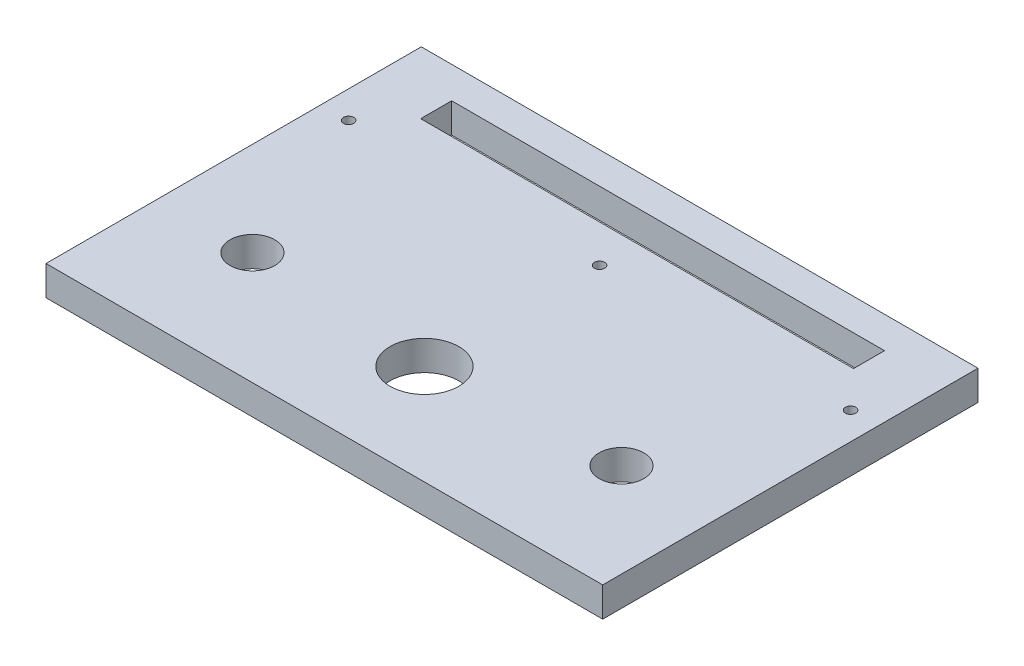
SolidWorks part; units mm, degrees
ref_plane "Front Plane" through (0, 0, 0) normal (0, 0, 1) x (1, 0, 0)
ref_plane "Top Plane" through (0, 0, 0) normal (0, 1, 0) x (1, 0, 0)
ref_plane "Right Plane" through (0, 0, 0) normal (1, 0, 0) x (0, 0, -1)
sketch "Sketch1" plane through (0, 0, 0) normal (0, 1, 0) x (1, 0, 0)
  line L2 (-89, 60) -> (-89, -60)
  line L3 (-89, -60) -> (89, -60)
  line L4 (89, 60) -> (89, -60)
  line L5 (-89, 60) -> (89, -60) construction
  line L6 (-89, -60) -> (89, 60) construction
  line L10 (0, 60) -> (0, -60) construction
  line L11 (-89, 60) -> (89, 60)
  line L12 (-69.2, 49.9) -> (-69.2, 40)
  line L13 (-69.2, 40) -> (69.2, 40)
  line L14 (69.2, 40) -> (69.2, 49.9)
  line L15 (69.2, 49.9) -> (-69.2, 49.9)
  circle A0 centre (0, -28) radius 11
  circle A1 centre (-59, -24) radius 7.15
  circle A2 centre (59, -24) radius 7.15
  point P0 (0, 0)
  point P19 (0, 49.9)
  dimension "D5" = 22
  dimension "D7" = 14.3
  dimension "D8" = 59
  dimension "D9" = 4
  dimension "D1" = 178
  dimension "D2" = 120
  dimension "D3" = 20
  dimension "D4" = 9.9
  dimension "D6" = 36
  dimension "D10" = 138.4
extrude "Boss-Extrude1" add sketch "Sketch1" along normal blind 9.5
hole_wizard "M4 Tapped Hole1" positions "Sketch2" profile "Sketch3" tap size "M4" standard "ISO" end condition through all
sketch "Sketch2" plane through (0, 9.5, 0) normal (0, 1, 0) x (1, 0, 0)
  line L0 (0, 60) -> (0, -60) construction
  line L3 (-89, 60) -> (-89, -60) construction
  line L5 (89, 60) -> (-89, 60) construction
  line L6 (-89, -60) -> (89, -60) construction
  line L7 (-69.2, 40) -> (69.2, 40) construction
  point P0 (-80.25, 28)
  point P2 (0, 28)
  point P18 (80.25, 28)
  dimension "D1" = 8.75
  dimension "D2" = 12
sketch "Sketch3" plane through (-80.25, 9.5, -28) normal (1, 0, 0) x (0, 0, 1)
  line L0 (0, 0) -> (0, 9.5)
  line L1 (0, 9.5) -> (1.65, 9.5)
  line L2 (1.65, 9.5) -> (1.65, 0)
  line L5 (1.65, 0) -> (0, 0)
  line L11 (0, -6.35) -> (0, 107.95) construction
  dimension "Thru Tap Drill Dia." = 3.3
  dimension "Thru Tap Drill Depth" = 9.5
cosmetic thread "Hole Thread1" parameters "D2"=4
cosmetic thread "Hole Thread2" parameters "D2"=4
cosmetic thread "Hole Thread3" parameters "D2"=4
